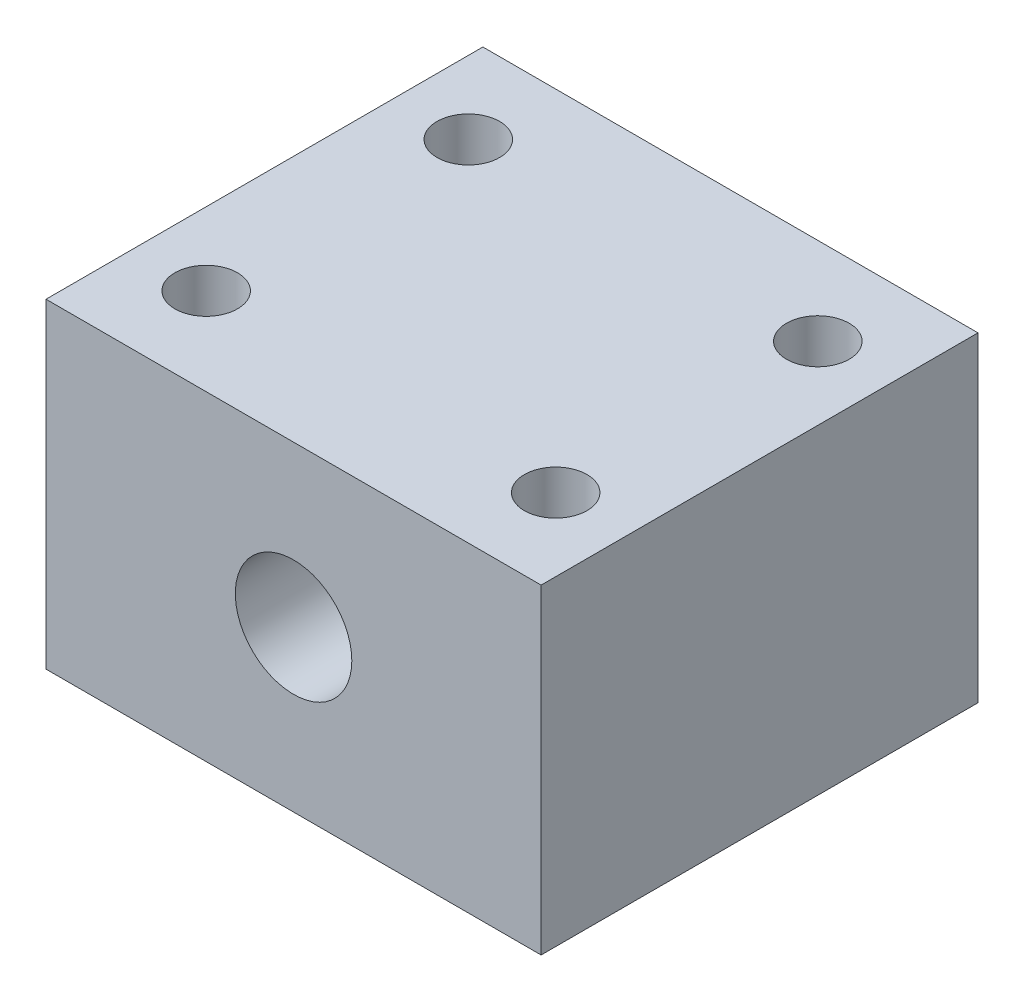
SolidWorks part; units mm, degrees
ref_plane "前视基准面" through (0, 0, 0) normal (0, 0, 1) x (1, 0, 0)
ref_plane "上视基准面" through (0, 0, 0) normal (0, 1, 0) x (1, 0, 0)
ref_plane "右视基准面" through (0, 0, 0) normal (1, 0, 0) x (0, 0, -1)
sketch "草图1" plane through (0, 0, 0) normal (0, 1, 0) x (1, 0, 0)
  line L1 (-17, 15) -> (17, 15)
  line L2 (-17, 15) -> (-17, -15)
  line L3 (-17, -15) -> (17, -15)
  line L4 (17, 15) -> (17, -15)
  line L5 (-17, 15) -> (17, -15) construction
  line L6 (-17, -15) -> (17, 15) construction
  point P0 (0, 0)
  dimension "D1" = 34
  dimension "D2" = 30
extrude "凸台-拉伸1" add sketch "草图1" along normal blind 22
sketch "草图2" plane through (0, 22, 0) normal (0, 1, 0) x (1, 0, 0)
  line L1 (-12, 9) -> (12, 9) construction
  line L2 (-12, 9) -> (-12, -9) construction
  line L3 (-12, -9) -> (12, -9) construction
  line L4 (12, 9) -> (12, -9) construction
  line L5 (-12, 9) -> (12, -9) construction
  line L6 (-12, -9) -> (12, 9) construction
  circle A0 centre (-12, 9) radius 2.15
  circle A1 centre (12, 9) radius 2.15
  circle A2 centre (12, -9) radius 2.15
  circle A3 centre (-12, -9) radius 2.15
  point P0 (0, 0)
  dimension "D3" = 4.3
  dimension "D4" = 4.3
  dimension "D5" = 4.3
  dimension "D6" = 4.3
  dimension "D1" = 24
  dimension "D2" = 18
extrude "切除-拉伸1" cut sketch "草图2" against normal through all
sketch "草图3" plane through (0, 0, 15) normal (0, 0, 1) x (1, 0, 0)
  line L0 (-17, 22) -> (17, 22) construction
  circle A0 centre (0, 11) radius 4
  point P4 (0, 0)
  dimension "D1" = 8
  dimension "D2" = 11
extrude "切除-拉伸2" cut sketch "草图3" against normal through all
